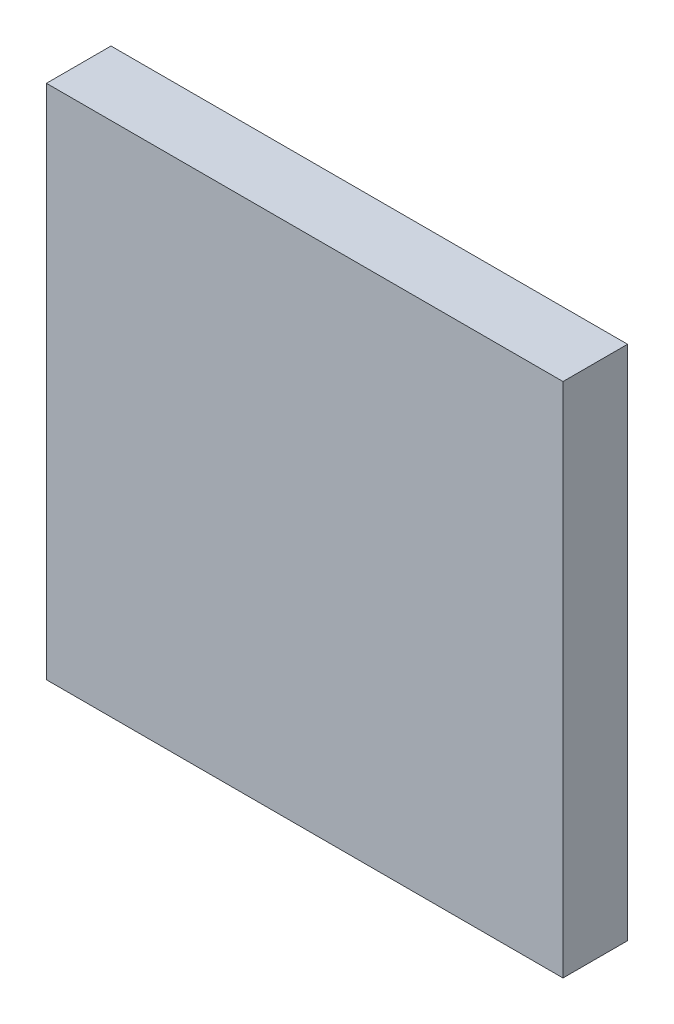
SolidWorks part; units mm, degrees
ref_plane "Front Plane" through (0, 0, 0) normal (0, 0, 1) x (1, 0, 0)
ref_plane "Top Plane" through (0, 0, 0) normal (0, 1, 0) x (1, 0, 0)
ref_plane "Right Plane" through (0, 0, 0) normal (1, 0, 0) x (0, 0, -1)
sketch "Sketch1" plane through (0, 0, 0) normal (0, 0, 1) x (1, 0, 0)
  line L1 (-20, 20) -> (20, 20)
  line L2 (-20, 20) -> (-20, -20)
  line L3 (-20, -20) -> (20, -20)
  line L4 (20, 20) -> (20, -20)
  line L5 (-20, 20) -> (20, -20) construction
  line L6 (-20, -20) -> (20, 20) construction
  point P0 (0, 0)
  dimension "D1" = 40
  dimension "D2" = 40
extrude "Boss-Extrude1" add sketch "Sketch1" along normal blind 5
